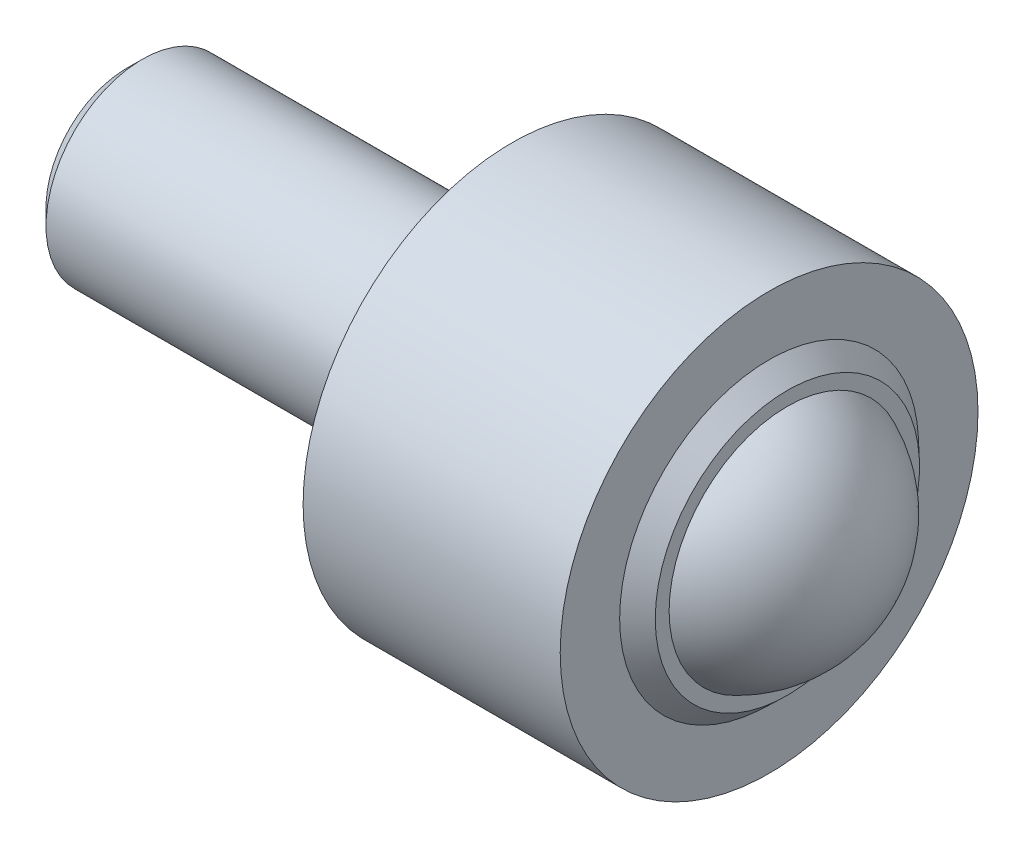
SolidWorks part; units mm, degrees
ref_plane "Front" through (0, 0, 0) normal (0, 0, 1) x (1, 0, 0)
ref_plane "Top" through (0, 0, 0) normal (0, 1, 0) x (1, 0, 0)
ref_plane "Right" through (0, 0, 0) normal (1, 0, 0) x (0, 0, -1)
sketch "草图1" plane through (0, 0, 0) normal (1, 0, 0) x (0, 0, -1)
  circle A0 centre (0, 0) radius 3
  dimension "D1" = 6
extrude "凸台-拉伸1" add sketch "草图1" along normal blind 12
cosmetic thread "装饰螺纹线1" parameters "D2"=4.917
sketch "草图2" plane through (12, 0, 0) normal (1, 0, 0) x (0, 0, -1)
  circle A0 centre (0, 0) radius 6.5
  dimension "D1" = 13
extrude "凸台-拉伸2" add sketch "草图2" along normal blind 8
sketch "草图3" plane through (0, 0, 0) normal (0, 1, 0) x (1, 0, 0)
  line L0 (0, 0) -> (29.5776, 0) construction
  line L1 (20, -6.5) -> (20, 6.5) construction
  line L2 (15, 0) -> (23, 0)
  line L3 (20, 4.6509) -> (20.5681, 4.111)
  line L4 (20.5681, 4.111) -> (20.5681, 3.6798)
  line L5 (20, 4.6509) -> (20, 3.873)
  arc A0 (23, 0) -> (20.5681, 3.6798) centre (19, 0) ccw
  arc A1 (20, 3.873) -> (15, 0) centre (19, 0) ccw
  dimension "D1" = 8
  dimension "D2" = 1
revolve "旋转2" add sketch "草图3" angle 360 about L2
chamfer "倒角1" distance 0.5 angle 45 1 edges at (0, 0, -3)
